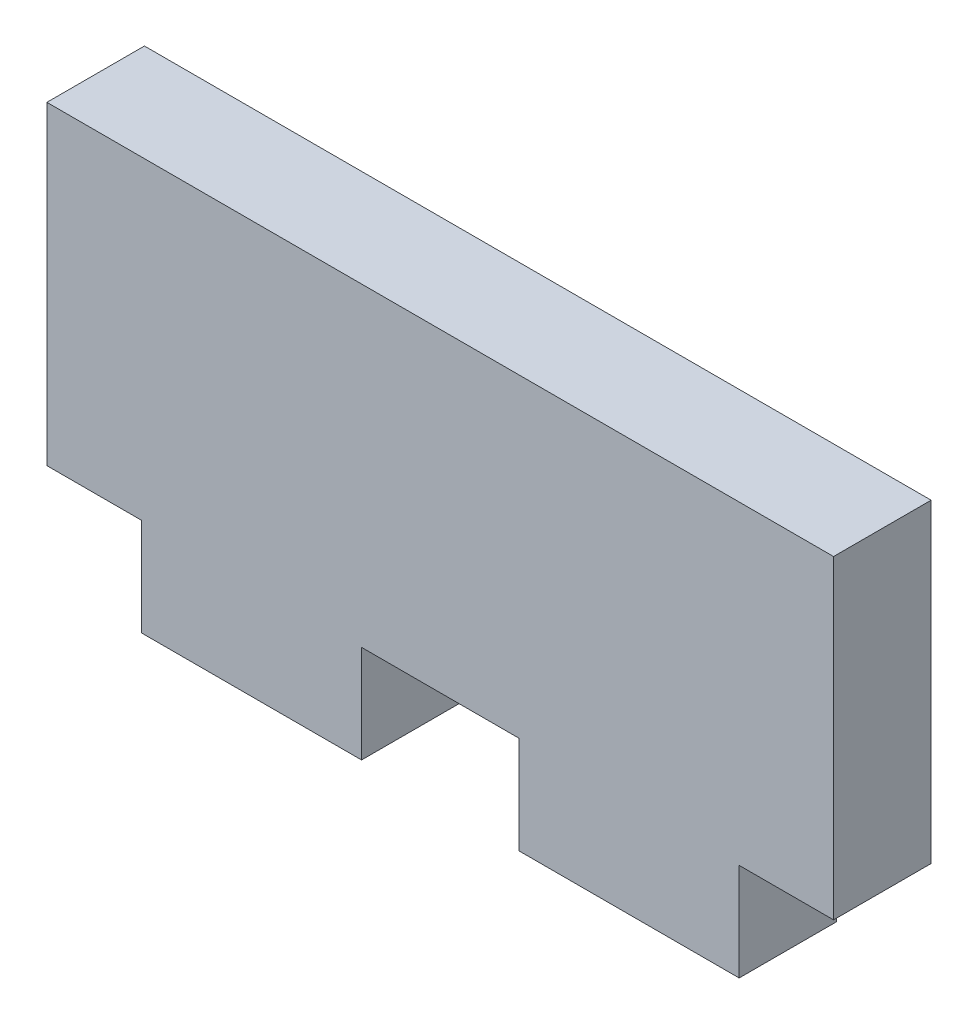
SolidWorks part; units mm, degrees
ref_plane "前视基准面" through (0, 0, 0) normal (0, 0, 1) x (1, 0, 0)
ref_plane "上视基准面" through (0, 0, 0) normal (0, 1, 0) x (1, 0, 0)
ref_plane "右视基准面" through (0, 0, 0) normal (1, 0, 0) x (0, 0, -1)
sketch "草图1" plane through (0, 0, 0) normal (0, 0, 1) x (1, 0, 0)
  line L0 (2.5, -5) -> (2.5, -8.1)
  line L1 (-12.5, -5) -> (12.5, -5)
  line L2 (-12.5, -5) -> (-12.5, 5)
  line L3 (-12.5, 5) -> (12.5, 5)
  line L4 (12.5, -5) -> (12.5, 5)
  line L5 (-12.5, -5) -> (12.5, 5) construction
  line L6 (-12.5, 5) -> (12.5, -5) construction
  line L7 (-9.5, -5) -> (-2.5, -5)
  line L8 (-9.5, -5) -> (-9.5, -8.1)
  line L9 (-9.5, -8.1) -> (-2.5, -8.1)
  line L10 (-2.5, -5) -> (-2.5, -8.1)
  line L11 (0, 5) -> (0, -5) construction
  line L12 (9.5, -8.1) -> (2.5, -8.1)
  line L13 (9.5, -5) -> (9.5, -8.1)
  line L14 (9.5, -5) -> (2.5, -5)
  point P0 (0, 0)
  dimension "D1" = 3.1
  dimension "D2" = 7
  dimension "D3" = 25
  dimension "D4" = 10
  dimension "D5" = 5
extrude "凸台-拉伸1" add sketch "草图1" along normal blind 3.1 contours L1 L4 L3 L2 | L10 L1 L8 L9 | L13 L1 L0 L12
